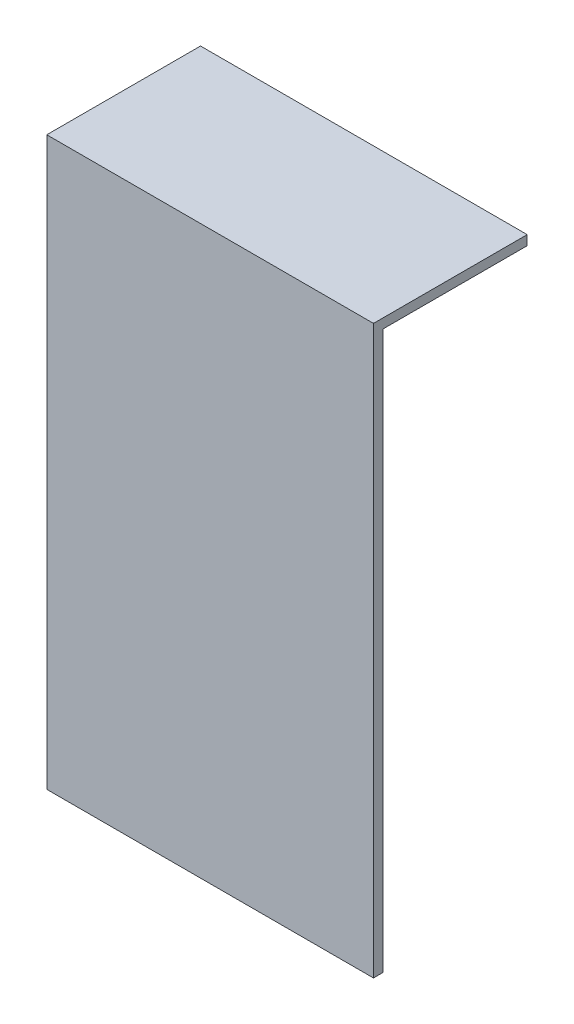
SolidWorks part; units mm, degrees
other "Markup1"
sketch "Sketch3" plane through (-43.18, 149.86, 1.27) normal (-0.8564, 0.3869, 0.342) x (0.4812, 0.3579, 0.8002)
material "PPE"
ref_plane "Front Plane" through (0, 0, 0) normal (0, 0, 1) x (1, 0, 0)
ref_plane "Top Plane" through (0, 0, 0) normal (0, 1, 0) x (1, 0, 0)
ref_plane "Right Plane" through (0, 0, 0) normal (1, 0, 0) x (0, 0, -1)
sketch "Sketch1" plane through (0, 0, 0) normal (0, 1, 0) x (1, 0, 0)
  line L1 (-43.18, -1.27) -> (43.18, -1.27)
  line L2 (-43.18, -1.27) -> (-43.18, 1.27)
  line L3 (-43.18, 1.27) -> (43.18, 1.27)
  line L4 (43.18, -1.27) -> (43.18, 1.27)
  line L5 (-43.18, -1.27) -> (43.18, 1.27) construction
  line L6 (-43.18, 1.27) -> (43.18, -1.27) construction
  point P0 (0, 0)
  dimension "D1" = 86.36
  dimension "D2" = 2.54
extrude "Boss-Extrude1" add sketch "Sketch1" along normal blind 149.86
sketch "Sketch2" plane through (0, 0, -1.27) normal (0, 0, -1) x (-1, 0, 0)
  line L0 (43.18, 149.86) -> (43.18, 0) construction
  line L1 (-43.18, 149.86) -> (43.18, 149.86)
  line L2 (-43.18, 149.86) -> (-43.18, 147.32)
  line L3 (-43.18, 147.32) -> (43.18, 147.32)
  line L4 (43.18, 149.86) -> (43.18, 147.32)
  dimension "D1" = 2.54
extrude "Boss-Extrude2" add sketch "Sketch2" along normal blind 38.1
scale "Scale1" [suppressed]
